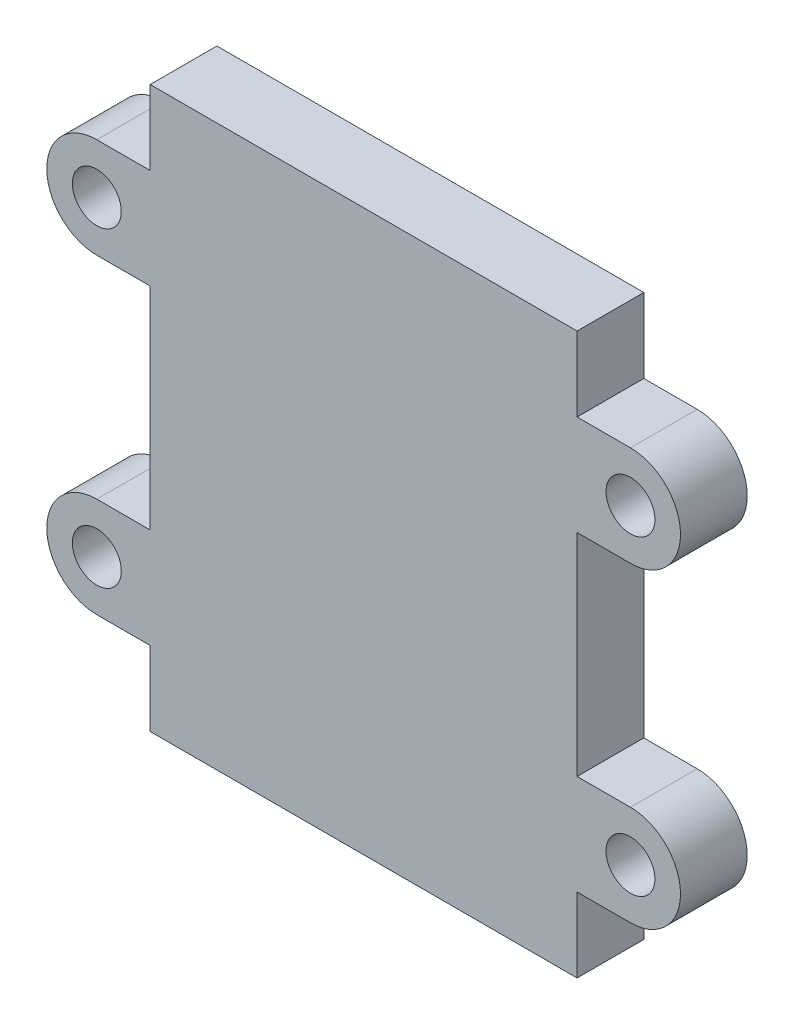
SolidWorks part; units mm, degrees
ref_plane "前视基准面" through (0, 0, 0) normal (0, 0, 1) x (1, 0, 0)
ref_plane "上视基准面" through (0, 0, 0) normal (0, 1, 0) x (1, 0, 0)
ref_plane "右视基准面" through (0, 0, 0) normal (1, 0, 0) x (0, 0, -1)
sketch "草图1" plane through (0, 0, 0) normal (0, 0, 1) x (1, 0, 0)
  line L0 (-9.6, -12.6) -> (-9.6, 12.6)
  line L1 (-8, -11) -> (8, -11) construction
  line L2 (-8, -11) -> (-8, 11) construction
  line L3 (-8, 11) -> (8, 11) construction
  line L4 (8, -11) -> (8, 11) construction
  line L5 (-8, -11) -> (8, 11) construction
  line L6 (-8, 11) -> (8, -11) construction
  line L7 (-9.6, 12.6) -> (9.6, 12.6)
  line L8 (9.6, -12.6) -> (9.6, 12.6)
  line L9 (-9.6, -12.6) -> (9.6, -12.6)
  line L12 (0, 0) -> (0, 18.7905) construction
  line L14 (0, 0) -> (13.8633, 0) construction
  point P0 (0, 0)
  dimension "D2" = 16
  dimension "D4" = 22
  dimension "D1" = 1.6
extrude "凸台-拉伸1" add sketch "草图1" along normal blind 3
sketch "草图3" plane through (0, 0, 3) normal (0, 0, 1) x (1, 0, 0)
  line L2 (0, 0) -> (8.1969, 0) construction
  line L6 (0, 0) -> (0, 14.137) construction
  line L10 (12, 9.25) -> (9.6, 9.25)
  line L11 (9.6, -12.6) -> (9.6, 12.6) construction
  line L12 (9.6, 9.25) -> (9.6, 4.75)
  line L13 (9.6, 4.75) -> (12, 4.75)
  line L14 (9.6, -9.25) -> (9.6, -4.75)
  line L15 (12, -9.25) -> (9.6, -9.25)
  line L16 (9.6, -4.75) -> (12, -4.75)
  line L17 (-12, -9.25) -> (-9.6, -9.25)
  line L18 (-9.6, -4.75) -> (-12, -4.75)
  line L19 (-9.6, -9.25) -> (-9.6, -4.75)
  line L20 (-9.6, 9.25) -> (-9.6, 4.75)
  line L21 (-12, 9.25) -> (-9.6, 9.25)
  line L22 (-9.6, 4.75) -> (-12, 4.75)
  circle A0 centre (12, 7) radius 1.1
  arc A1 (12, 9.25) -> (12, 4.75) centre (12, 7) cw
  circle A4 centre (12, -7) radius 1.1
  arc A5 (12, -9.25) -> (12, -4.75) centre (12, -7) ccw
  circle A6 centre (-12, -7) radius 1.1
  arc A7 (-12, -9.25) -> (-12, -4.75) centre (-12, -7) cw
  circle A8 centre (-12, 7) radius 1.1
  arc A9 (-12, 9.25) -> (-12, 4.75) centre (-12, 7) ccw
  dimension "D1" = 2.2
  dimension "D2" = 2.25
  dimension "D3" = 2.4
  dimension "D4" = 7
extrude "凸台-拉伸2" add sketch "草图3" against normal through all
mirror "镜向1" about plane through (0, 0, 0) normal (0, 1, 0) of "凸台-拉伸2"
sketch "草图4" plane through (-9.6, 3, 0) normal (-1, 0, 0) x (0, 1, 0)
  circle A0 centre (-3, 0) radius 1.15
  dimension "D1" = 2.3
extrude "切除-拉伸1" cut sketch "草图4" against normal blind 7
sketch "草图5" plane through (0, 0, 0) normal (0, 0, -1) x (-1, 0, 0)
  circle A0 centre (0, 0) radius 2.5
  dimension "D1" = 5
extrude "凸台-拉伸3" add sketch "草图5" along normal blind 3
